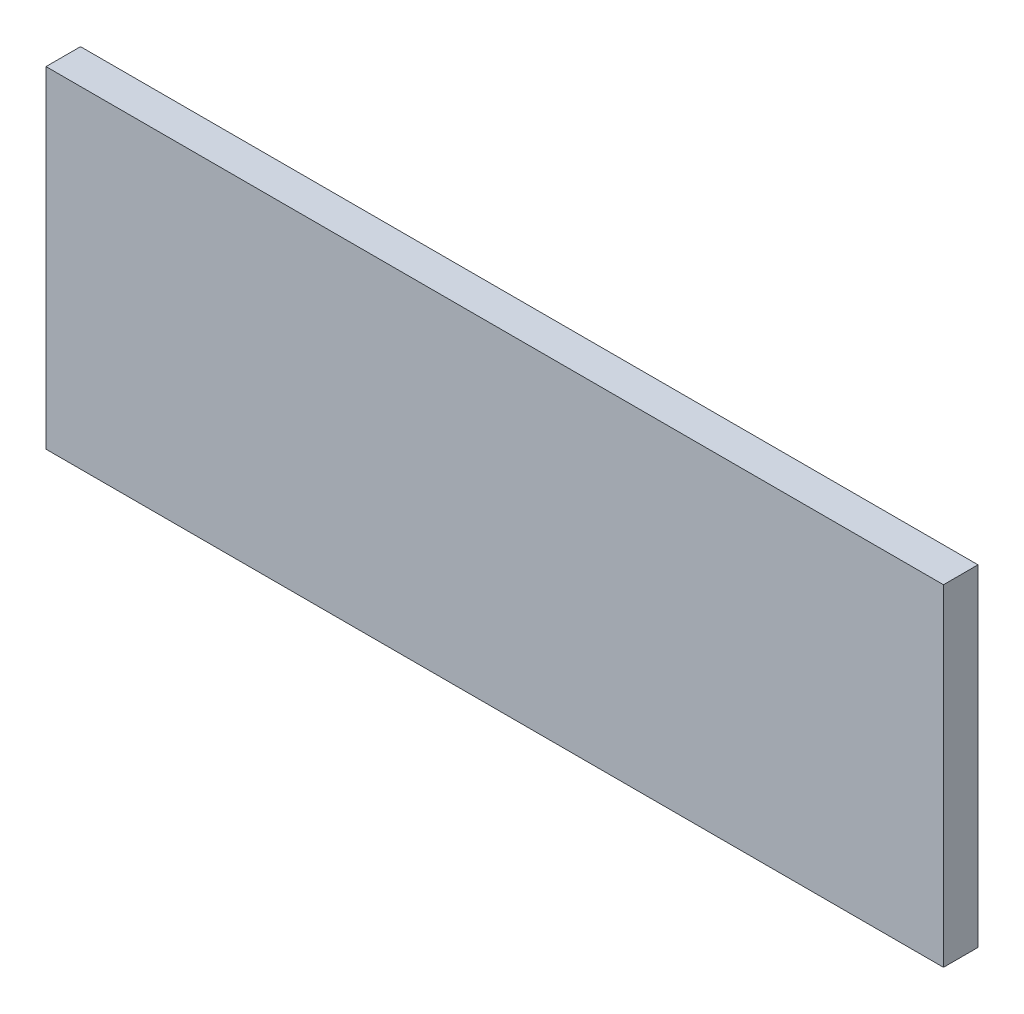
SolidWorks part; units mm, degrees
ref_plane "Front Plane" through (0, 0, 0) normal (0, 0, 1) x (1, 0, 0)
ref_plane "Top Plane" through (0, 0, 0) normal (0, 1, 0) x (1, 0, 0)
ref_plane "Right Plane" through (0, 0, 0) normal (1, 0, 0) x (0, 0, -1)
sketch "Sketch1" plane through (0, 0, 0) normal (0, 0, 1) x (1, 0, 0)
  line L1 (0, 0) -> (33.02, 0)
  line L2 (0, 0) -> (0, 12.192)
  line L3 (0, 12.192) -> (33.02, 12.192)
  line L4 (33.02, 0) -> (33.02, 12.192)
  dimension "D1" = 33.02
  dimension "D2" = 12.192
extrude "Boss-Extrude1" add sketch "Sketch1" along normal blind 1.27
